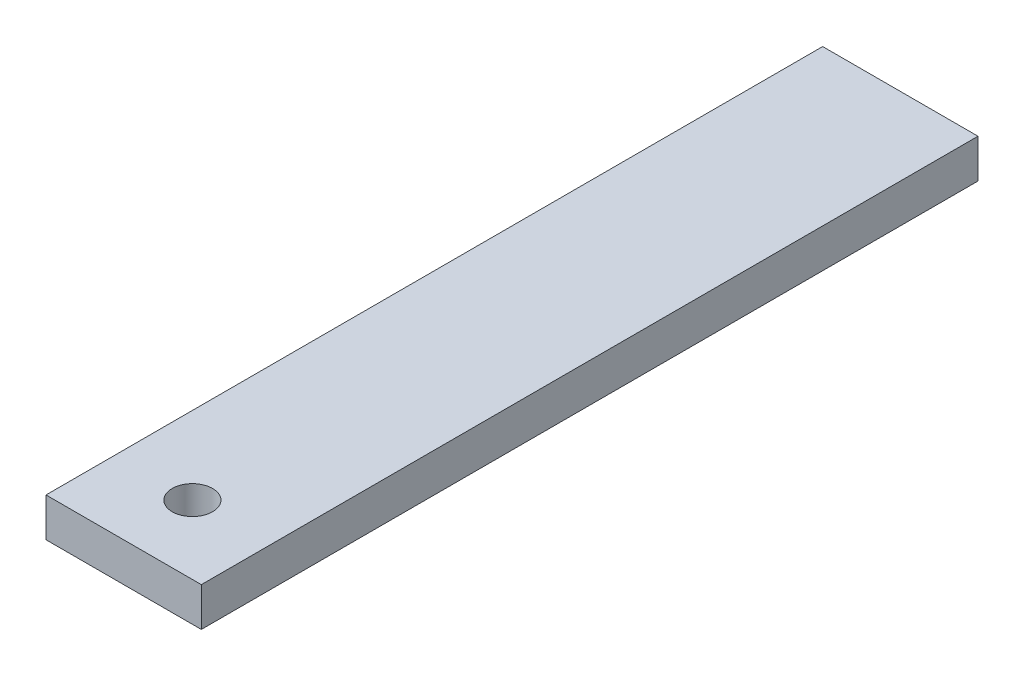
SolidWorks part; units mm, degrees
ref_plane "Front Plane" through (0, 0, 0) normal (0, 0, 1) x (1, 0, 0)
ref_plane "Top Plane" through (0, 0, 0) normal (0, 1, 0) x (1, 0, 0)
ref_plane "Right Plane" through (0, 0, 0) normal (1, 0, 0) x (0, 0, -1)
sketch "Sketch1" plane through (0, 0, 0) normal (0, 1, 0) x (1, 0, 0)
  line L1 (0, 0) -> (25.4, 0)
  line L2 (0, 0) -> (0, 127)
  line L3 (0, 127) -> (25.4, 127)
  line L4 (25.4, 0) -> (25.4, 127)
  circle A0 centre (12.7, 11.2387) radius 3.302
  point P7 (12.7, 0)
  point P8 (0, 0)
  dimension "D3" = 6.604
  dimension "D1" = 127
  dimension "D2" = 25.4
extrude "Boss-Extrude1" add sketch "Sketch1" along normal blind 6.35
